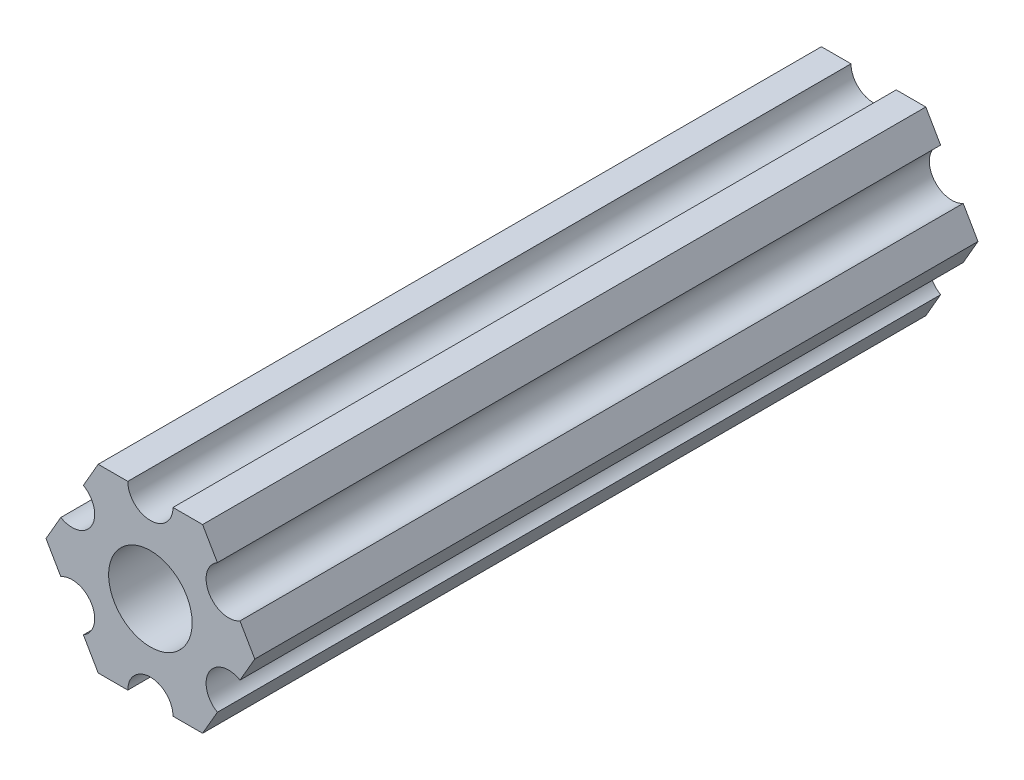
SolidWorks part; units mm, degrees
ref_plane "Front Plane" through (0, 0, 0) normal (0, 0, 1) x (1, 0, 0)
ref_plane "Top Plane" through (0, 0, 0) normal (0, 1, 0) x (1, 0, 0)
ref_plane "Right Plane" through (0, 0, 0) normal (1, 0, 0) x (0, 0, -1)
ref_plane "Plane1" through (0, 0, 0) normal (0, 0, -1) x (-1, 0, 0)
sketch "Sketch1" plane through (0, 0, 0) normal (0, 0, -1) x (-1, 0, 0)
  line L0 (-4.7055, -4.5498) -> (-3.6662, -6.35)
  line L1 (-3.6662, -6.35) -> (-1.5875, -6.35)
  line L2 (1.5875, -6.35) -> (3.6662, -6.35)
  line L3 (3.6662, -6.35) -> (4.7055, -4.5498)
  line L4 (6.293, -1.8002) -> (7.3323, 0)
  line L5 (7.3323, 0) -> (6.293, 1.8002)
  line L6 (4.7055, 4.5498) -> (3.6662, 6.35)
  line L7 (3.6662, 6.35) -> (1.5875, 6.35)
  line L8 (-1.5875, 6.35) -> (-3.6662, 6.35)
  line L9 (-3.6662, 6.35) -> (-4.7055, 4.5498)
  line L10 (-6.293, 1.8002) -> (-7.3323, 0)
  line L11 (-7.3323, 0) -> (-6.293, -1.8002)
  circle A0 centre (0, 0) radius 2.9337
  arc A1 (-6.293, -1.8002) -> (-4.7055, -4.5498) centre (-5.4993, -3.175) cw
  arc A2 (-1.5875, -6.35) -> (1.5875, -6.35) centre (0, -6.35) cw
  arc A3 (4.7055, -4.5498) -> (6.293, -1.8002) centre (5.4993, -3.175) cw
  arc A4 (6.293, 1.8002) -> (4.7055, 4.5498) centre (5.4993, 3.175) cw
  arc A5 (1.5875, 6.35) -> (-1.5875, 6.35) centre (0, 6.35) cw
  arc A6 (-4.7055, 4.5498) -> (-6.293, 1.8002) centre (-5.4993, 3.175) cw
extrude "Boss-Extrude1" add sketch "Sketch1" along normal blind 50.8
